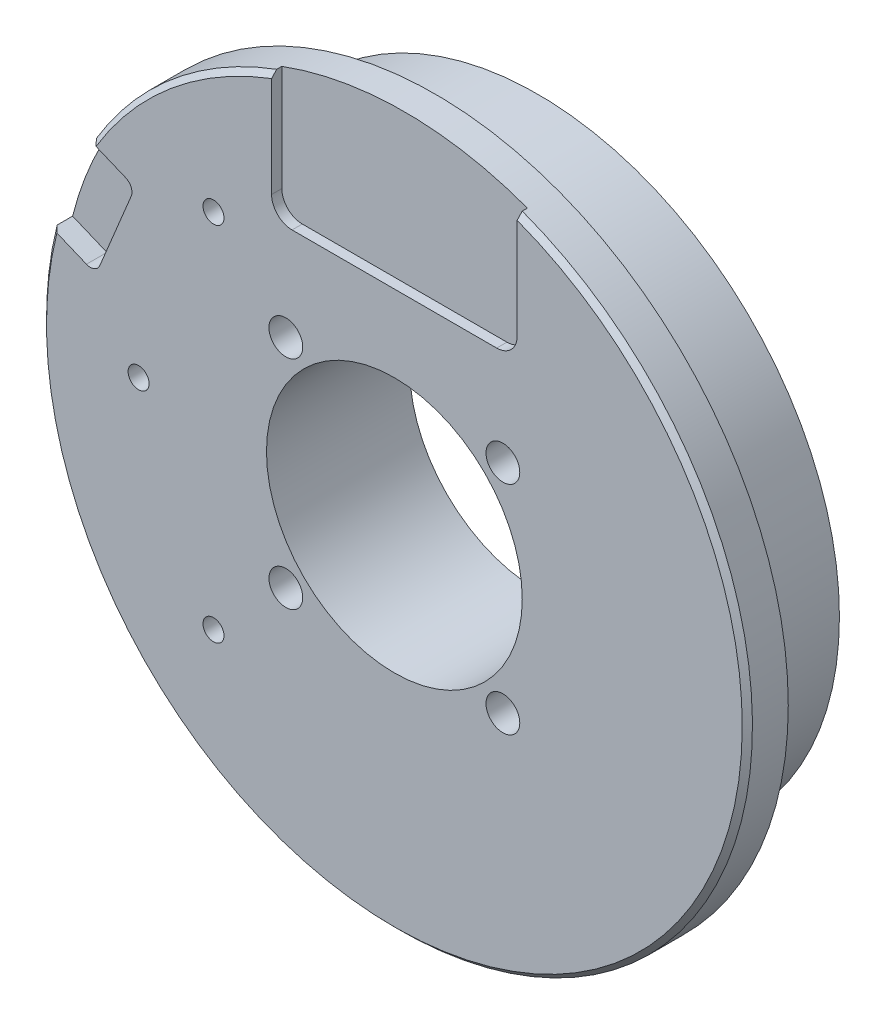
SolidWorks part; units mm, degrees
ref_plane "Front Plane" through (0, 0, 0) normal (0, 0, 1) x (1, 0, 0)
ref_plane "Top Plane" through (0, 0, 0) normal (0, 1, 0) x (1, 0, 0)
ref_plane "Right Plane" through (0, 0, 0) normal (1, 0, 0) x (0, 0, -1)
sketch "Sketch1" plane through (0, 0, 0) normal (0, 0, 1) x (1, 0, 0)
  circle A0 centre (0, 0) radius 29.5
  dimension "D1" = 59
extrude "Boss-Extrude1" add sketch "Sketch1" along normal blind 10
sketch "Sketch2" plane through (0, 0, 10) normal (0, 0, 1) x (1, 0, 0)
  circle A0 centre (0, 0) radius 34.5
  dimension "D1" = 69
extrude "Boss-Extrude2" add sketch "Sketch2" along normal blind 4
sketch "Sketch3" plane through (0, 0, 14) normal (0, 0, 1) x (1, 0, 0)
  circle A0 centre (0, 0) radius 12.5
  dimension "D1" = 25
extrude "Cut-Extrude1" cut sketch "Sketch3" against normal through all
hole_wizard "M4 Tapped Hole1" positions "Sketch4" profile "Sketch5" tap size "M4" standard "DIN" end condition through all
sketch "Sketch4" plane through (0, 0, 14) normal (0, 0, 1) x (1, 0, 0)
  line L0 (-10.6066, -10.6066) -> (10.6066, 10.6066) construction
  line L3 (-10.6066, 10.6066) -> (10.6066, -10.6066) construction
  circle A0 centre (0, 0) radius 15 construction
  point P0 (-10.6066, 10.6066)
  point P2 (10.6066, 10.6066)
  point P4 (10.6066, -10.6066)
  point P6 (-10.6066, -10.6066)
  dimension "D1" = 30
sketch "Sketch5" plane through (-10.6066, 10.6066, 14) normal (1, 0, 0) x (0, -1, 0)
  line L0 (0, 0) -> (0, 14)
  line L1 (0, 14) -> (1.65, 14)
  line L2 (1.65, 14) -> (1.65, 0)
  line L5 (1.65, 0) -> (0, 0)
  line L11 (0, -6.35) -> (0, 107.95) construction
  dimension "Thru Tap Drill Dia." = 3.3
  dimension "Thru Tap Drill Depth" = 14
cosmetic thread "Hole Thread1" parameters "D2"=4
cosmetic thread "Hole Thread2" parameters "D2"=4
cosmetic thread "Hole Thread3" parameters "D2"=4
cosmetic thread "Hole Thread4" parameters "D2"=4
hole_wizard "M2.5 Tapped Hole1" positions "Sketch7" profile "Sketch8" tap size "M2.5" standard "DIN"
sketch "Sketch7" plane through (0, 0, 14) normal (0, 0, 1) x (1, 0, 0)
  line L0 (-17.6777, 17.6777) -> (0, 0) construction
  line L1 (0, 0) -> (-25, 0) construction
  circle A0 centre (0, 0) radius 25 construction
  point P0 (-17.6777, -17.6777)
  point P2 (-25, 0)
  point P4 (-17.6777, 17.6777)
  dimension "D2" = 50
  dimension "D1" = 45
sketch "Sketch8" plane through (-17.6777, -17.6777, 14) normal (1, 0, 0) x (0, -1, 0)
  line L0 (0, 0) -> (0, 6.9659)
  line L1 (0, 6.9659) -> (1.025, 6.35)
  line L2 (1.025, 6.35) -> (1.025, 0)
  line L5 (1.025, 0) -> (0, 0)
  line L10 (0, 6.9659) -> (-1.025, 6.35) construction
  line L11 (0, -6.35) -> (0, 107.95) construction
  dimension "Tap Drill Dia." = 2.05
  dimension "Tap Drill Depth" = 6.35
  dimension "Drill Angle" = 118
cosmetic thread "Hole Thread5" parameters "D1"=5, "D2"=2.5
cosmetic thread "Hole Thread6" parameters "D1"=5, "D2"=2.5
cosmetic thread "Hole Thread7" parameters "D1"=5, "D2"=2.5
sketch "Sketch9" plane through (0, 0, 14) normal (0, 0, 1) x (1, 0, 0)
  line L0 (-33.4507, 8.4438) -> (-30.0917, 7.0524)
  line L1 (-28.7852, 7.5936) -> (-25.7237, 14.9847)
  line L2 (-26.2649, 16.2912) -> (-29.6239, 17.6826)
  line L3 (-31.8738, 13.2026) -> (0, 0) construction
  line L4 (-25, 0) -> (-17.6777, 17.6777) construction
  circle A0 centre (0, 0) radius 34.5 construction
  arc A1 (-30.0917, 7.0524) -> (-28.7852, 7.5936) centre (-29.7091, 7.9763) ccw
  arc A2 (-25.7237, 14.9847) -> (-26.2649, 16.2912) centre (-26.6476, 15.3674) ccw
  arc A4 (-29.6239, 17.6826) -> (-33.4507, 8.4438) centre (0, 0) ccw
  point P11 (-21.3388, 8.8388)
  dimension "D3" = 1
  dimension "D1" = 10
  dimension "D2" = 5
chamfer "Chamfer1" distance 0.5 angle 45 1 edges at (34.5, 0, 14)
extrude "Cut-Extrude2" cut sketch "Sketch9" against normal blind 2
sketch "Sketch10" plane through (0, 0, 14) normal (0, 0, 1) x (1, 0, 0)
  line L0 (0, 20) -> (0, 0) construction
  line L1 (-5, 22) -> (5, 22)
  line L2 (-6.5, 20.5) -> (-6.5, 19.5)
  line L3 (-5, 18) -> (5, 18)
  line L4 (6.5, 20.5) -> (6.5, 19.5)
  line L5 (-6.5, 18) -> (6.5, 22) construction
  arc A0 (5, 22) -> (6.5, 20.5) centre (5, 20.5) cw
  arc A1 (5, 18) -> (6.5, 19.5) centre (5, 19.5) ccw
  arc A2 (-6.5, 19.5) -> (-5, 18) centre (-5, 19.5) ccw
  arc A3 (-5, 22) -> (-6.5, 20.5) centre (-5, 20.5) ccw
  point P13 (6.5, 18)
  point P19 (-6.5, 22)
  dimension "D4" = 1.5
  dimension "D1" = 4
  dimension "D2" = 13
  dimension "D3" = 20
extrude "Cut-Extrude3" [suppressed] cut sketch "Sketch10" against normal blind 2
sketch "Sketch11" plane through (0, 0, 14) normal (0, 0, 1) x (1, 0, 0)
  line L0 (-12, 32.3458) -> (-12, 22)
  line L1 (-10, 20) -> (10, 20)
  line L2 (12, 22) -> (12, 32.3458)
  line L3 (0, 0) -> (0, 34.5) construction
  arc A0 (-33.4507, 8.4438) -> (-29.6239, 17.6826) centre (0, 0) ccw construction
  arc A1 (12, 32.3458) -> (-12, 32.3458) centre (0, 0) ccw
  arc A2 (10, 20) -> (12, 22) centre (10, 22) ccw
  arc A3 (-12, 22) -> (-10, 20) centre (-10, 22) ccw
  point P8 (12, 23.9301)
  point P11 (12, 20)
  point P14 (-12, 20)
  dimension "D3" = 2
  dimension "D1" = 24
  dimension "D2" = 20
extrude "Cut-Extrude4" cut sketch "Sketch11" against normal blind 1
